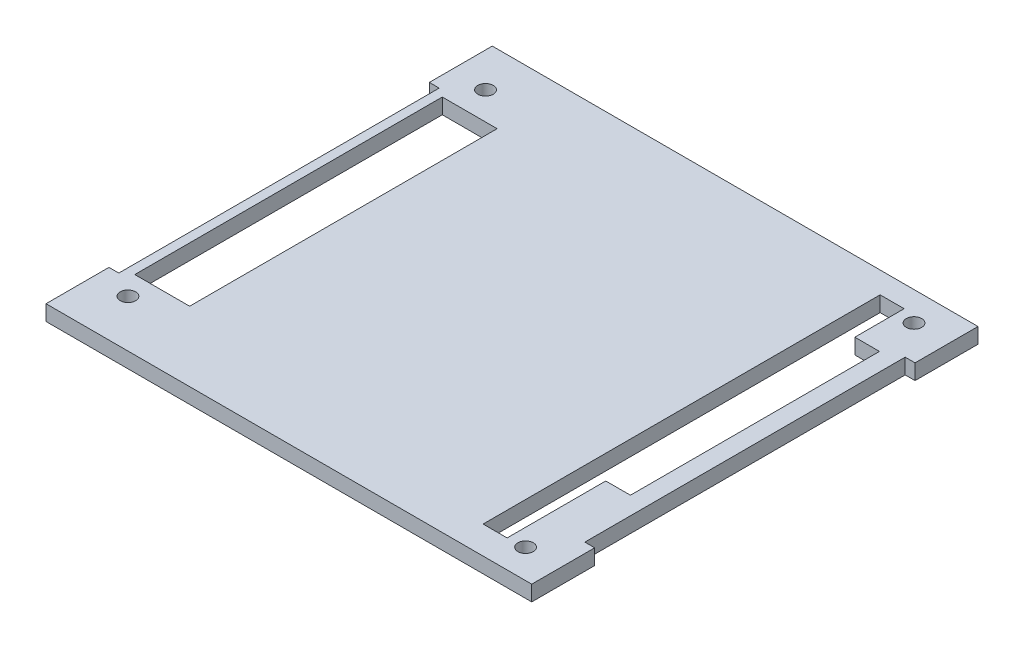
SolidWorks part; units mm, degrees
material "Delrin 2700 NC010, Low Viscosity Acetal Copolymer (SS)"
ref_plane "Front Plane" through (0, 0, 0) normal (0, 0, 1) x (1, 0, 0)
ref_plane "Top Plane" through (0, 0, 0) normal (0, 1, 0) x (1, 0, 0)
ref_plane "Right Plane" through (0, 0, 0) normal (1, 0, 0) x (0, 0, -1)
sketch "Sketch2" plane through (0, 0, 0) normal (0, 1, 0) x (1, 0, 0)
  line L1 (-50.0317, -45.9677) -> (50.0324, -45.9677)
  line L2 (-50.0317, -32.9997) -> (-50.0316, 33.0003)
  line L4 (45.9684, -32.9997) -> (45.9684, 33.0003)
  line L5 (45.9683, -47.9997) -> (45.9683, 48.0003) construction
  line L6 (50.0324, -45.9677) -> (48.0003, -45.9677)
  line L7 (48.0003, -45.9677) -> (48.0003, -32.9997)
  line L8 (48.0003, -32.9997) -> (45.9684, -32.9997)
  line L9 (48.0003, -32.9997) -> (48.0003, -45.9677) construction
  line L10 (45.9683, -32.9997) -> (48.0003, -32.9997) construction
  line L12 (-50.0316, 45.9683) -> (-52.0636, 45.9683)
  line L13 (-50.0316, 33.0003) -> (-50.0316, 45.9683)
  line L14 (-52.0636, 33.0003) -> (-50.0316, 33.0003)
  line L16 (-50.0316, 45.9683) -> (-52.0636, 45.9683)
  line L18 (-52.0636, 33.0003) -> (-50.0316, 33.0003)
  line L19 (-50.0317, -45.9677) -> (-50.0317, -32.9997)
  line L20 (-50.0317, -32.9997) -> (-52.0637, -32.9997)
  line L22 (-52.0637, -45.9677) -> (-50.0317, -45.9677)
  line L24 (-50.0317, -32.9997) -> (-52.0637, -32.9997)
  line L26 (-52.0637, -45.9677) -> (-50.0317, -45.9677)
  line L27 (45.9684, 33.0003) -> (48.0003, 33.0003)
  line L31 (-52.0636, 45.9683) -> (-52.0636, 33.0003)
  line L32 (-52.0636, 45.9683) -> (-52.0636, 33.0003)
  line L33 (-52.0637, -32.9997) -> (-52.0637, -45.9677)
  line L34 (-52.0637, -32.9997) -> (-52.0637, -45.9677)
  line L35 (45.9684, 33.0003) -> (45.9684, 45.9683) construction
  line L37 (48.0003, 33.0003) -> (48.0003, 45.9683)
  line L38 (48.0003, 45.9683) -> (45.9683, 45.9683)
  line L39 (45.9684, 45.9683) -> (48.0003, 45.9683) construction
  line L40 (48.0003, 33.0003) -> (48.0003, 45.9683) construction
  line L41 (45.9684, 33.0003) -> (48.0003, 33.0003) construction
  line L42 (-50.0316, 45.9683) -> (45.9683, 45.9683)
  point P0 (0, 0)
  point P7 (50.0324, 45.9683)
  point P14 (-50.0316, 55.3162)
  point P16 (-50.0316, 45.7883)
  dimension "D3" = 0
  dimension "D4" = 0
extrude "Boss-Extrude1" add sketch "Sketch2" along normal mid plane 3.175
sketch "Sketch4" plane through (0, 1.5875, 0) normal (0, 1, 0) x (1, 0, 0)
  line L1 (-50.0317, -32.9997) -> (-50.0316, 33.0003) construction
  point P2 (-44.9517, -45.9677)
  point P3 (45.8584, 0)
  point P5 (45.8584, -54.8577)
  point P6 (0, 0)
  line B0 (-36.8216, -31.62) -> (-48.1217, -31.62)
  line B1 (-36.8216, 31.73) -> (-36.8216, -31.62)
  line B2 (-48.1217, -31.62) -> (-48.1216, 31.73)
  line B3 (-48.1216, 31.73) -> (-36.8216, 31.73)
  line B4 (32.2683, -40.255) -> (37.2183, -40.255)
  line B5 (32.2683, 41.535) -> (32.2683, -40.255)
  line B6 (37.2184, 41.535) -> (32.2683, 41.535)
  line B7 (37.2184, 31.375) -> (37.2184, 41.535)
  line B8 (42.2983, 31.375) -> (37.2184, 31.375)
  line B9 (42.2983, -19.935) -> (42.2983, 31.375)
  line B10 (37.2183, -19.935) -> (42.2983, -19.935)
  line B11 (37.2183, -40.255) -> (37.2183, -19.935)
  line B12 (-50.0317, 45.085) -> (-50.0317, -45.085)
  line B13 (-50.0317, -45.085) -> (45.8584, -45.085)
  line B14 (45.8584, -45.085) -> (45.8583, 45.085)
  line B15 (45.8583, 45.085) -> (-50.0317, 45.085)
  circle B16 centre (40.7783, 40.005) radius 1.59
  circle B17 centre (-44.9517, 37.465) radius 1.59
  circle B18 centre (-44.9517, -36.195) radius 1.59
  circle B19 centre (40.7783, -40.005) radius 1.59
sketch_block_instance "Block-PC104 Block-1"
sketch_block "Block1"
extrude "Cut-Extrude2" cut sketch "Sketch4" against normal up to surface (3.175 mm away) contours B3 B2 B0 B1 | B17 | B4 B11 B10 B9 B8 B7 B6 B5 | B19 | B16 | B18 up to face at (-2.0317, -1.5875, -0.0003)
